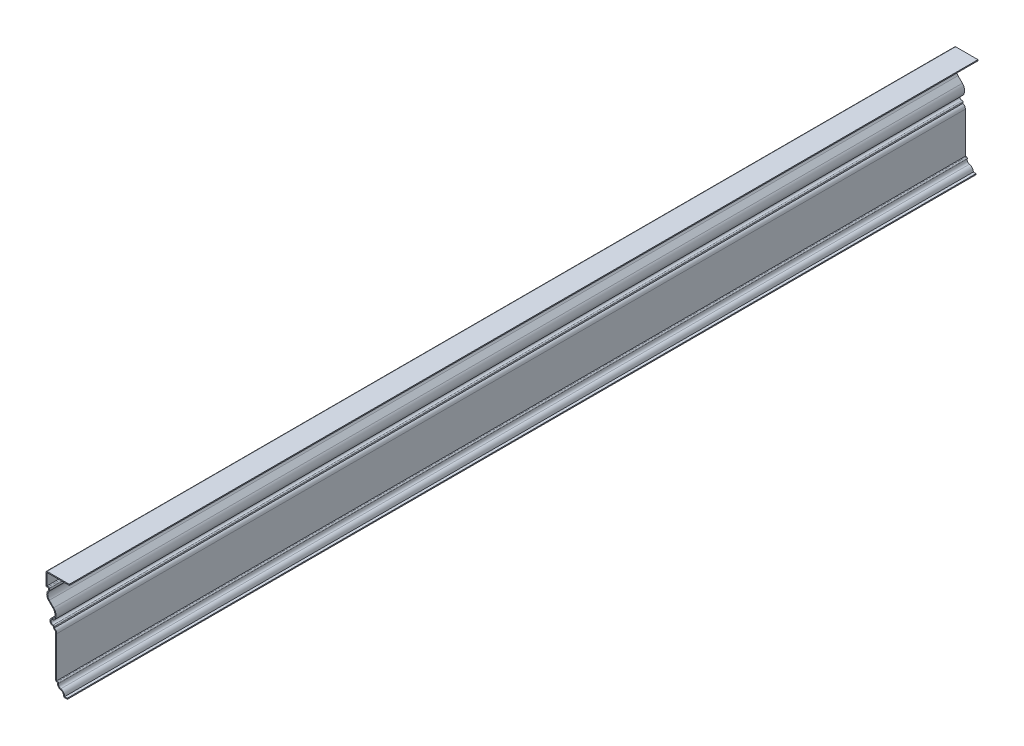
SolidWorks part; units mm, degrees
ref_plane "Front Plane" through (0, 0, 0) normal (0, 0, 1) x (1, 0, 0)
ref_plane "Top Plane" through (0, 0, 0) normal (0, 1, 0) x (1, 0, 0)
ref_plane "Right Plane" through (0, 0, 0) normal (1, 0, 0) x (0, 0, -1)
sketch "Sketch1" plane through (0, 0, 0) normal (0, 0, 1) x (1, 0, 0)
  line L0 (0, 0) -> (0, 44.2286) construction
  line L1 (0, 0) -> (-6.35, 0)
  line L2 (-15.875, 15.875) -> (-19.05, 15.875)
  line L3 (-19.05, 15.875) -> (-19.05, 84.1375)
  line L4 (-23.0188, 88.9) -> (-23.0188, 92.075)
  line L5 (-23.454, 117.0861) -> (-30.5958, 124.228)
  line L6 (-31.0311, 138.9204) -> (-31.0311, 142.0954)
  line L7 (-31.0311, 142.0954) -> (-34.925, 142.0954)
  line L8 (-34.925, 142.0954) -> (-34.925, 164.3204)
  line L9 (-34.925, 164.3204) -> (3.175, 164.3204)
  line L12 (-33.7344, 111.5329) -> (-33.7344, 119.1763) construction
  line L13 (-28.575, 93.6806) -> (-28.575, 99.7481) construction
  arc A0 (-6.35, 0) -> (-11.1125, 7.9375) centre (-12.4592, 1.732) ccw
  arc A1 (-11.1125, 7.9375) -> (-15.875, 15.875) centre (-9.7658, 14.143) cw
  arc A2 (-23.0188, 88.9) -> (-19.05, 84.1375) centre (-23.8919, 84.1375) cw
  arc A3 (-23.0188, 92.075) -> (-23.0188, 102.3937) centre (-23.4015, 97.2344) cw
  arc A4 (-23.0188, 102.3937) -> (-23.454, 117.0861) centre (-31.0311, 109.5091) ccw
  arc A5 (-30.5958, 124.228) -> (-31.0311, 138.9204) centre (-23.0188, 131.8051) cw
  point P28 (0, 0)
  point P29 (-23.0188, 116.0881)
  point P32 (-18.9141, 15.0803)
  point P35 (-23.0067, 102.0286)
  dimension "D6" = 6.35
  dimension "D12" = 5.5562
  dimension "D13" = 10.3187
  dimension "D17" = 5.1594
  dimension "D18" = 1.1906
  dimension "D1" = 19.05
  dimension "D2" = 6.35
  dimension "D3" = 3.175
  dimension "D4" = 15.875
  dimension "D5" = 9.525
  dimension "D7" = 15.875
  dimension "D8" = 3.9688
  dimension "D9" = 4.7625
  dimension "D10" = 3.175
  dimension "D11" = 68.2625
  dimension "D14" = 22.225
  dimension "D15" = 3.175
  dimension "D16" = 36.5125
  dimension "D19" = 38.1
  dimension "D20" = 164.3204
  dimension "D21" = 45
extrude "Extrude-Thin1" add sketch "Sketch1" against normal blind 1483.36 thin
fillet "Fillet1" radius 1.651 10 edges at (-6.35, 0, -741.68) (-13.0271, 17.526, -741.68) (-19.05, 15.875, -741.68) (-23.0188, 88.9, -741.68) (-21.3678, 94.3582, -741.68) (-22.4324, 100.621, -741.68) (-29.3801, 138.2628, -741.68) (-34.925, 142.0954, -741.68) (-29.3801, 143.7464, -741.68) (-34.925, 164.3204, -741.68)
